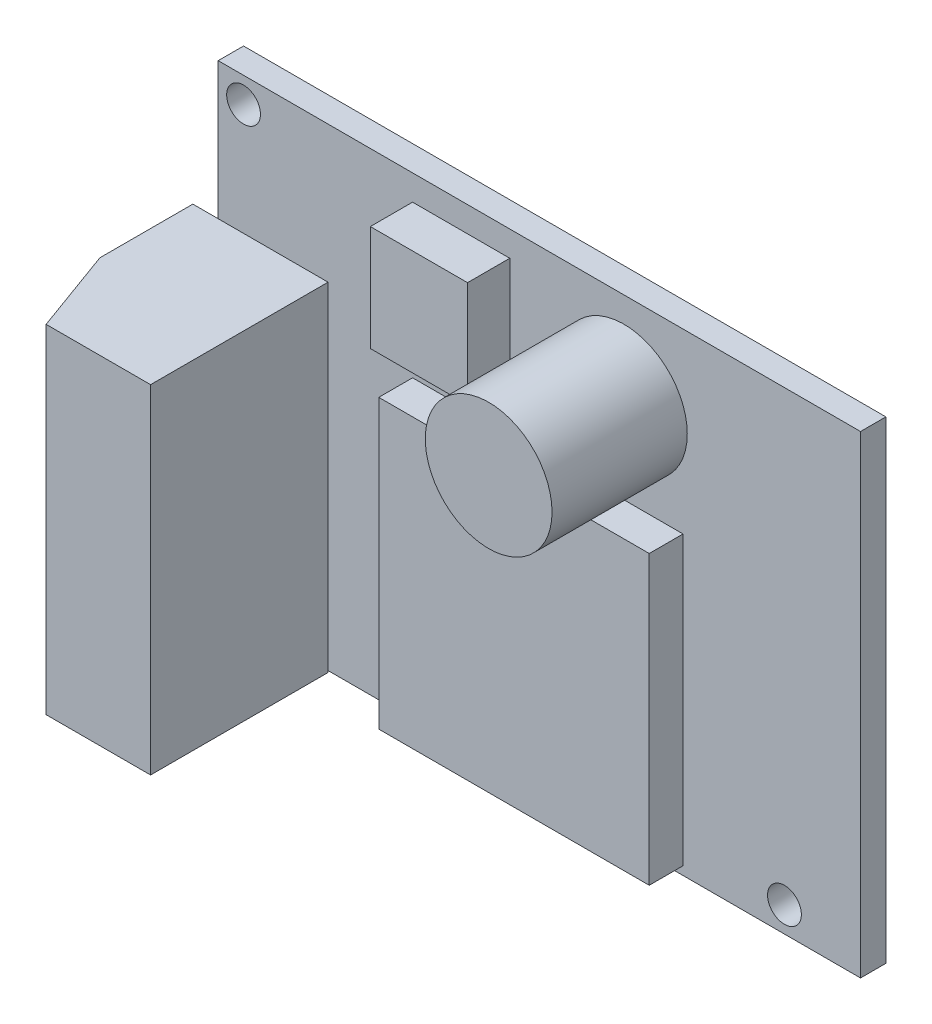
SolidWorks part; units mm, degrees
ref_plane "Front Plane" through (0, 0, 0) normal (0, 0, 1) x (1, 0, 0)
ref_plane "Top Plane" through (0, 0, 0) normal (0, 1, 0) x (1, 0, 0)
ref_plane "Right Plane" through (0, 0, 0) normal (1, 0, 0) x (0, 0, -1)
sketch "Sketch1" plane through (0, 0, 0) normal (0, 0, 1) x (1, 0, 0)
  line L1 (-19, 14) -> (19, 14)
  line L2 (-19, 14) -> (-19, -14)
  line L3 (-19, -14) -> (19, -14)
  line L4 (19, 14) -> (19, -14)
extrude "Boss-Extrude1" add sketch "Sketch1" along normal blind 1.5
sketch "Sketch2" plane through (0, 0, 1.5) normal (0, 0, 1) x (1, 0, 0)
  circle A0 centre (5, 8.75) radius 3.75
  point P8 (5, 8.75)
extrude "Boss-Extrude2" add sketch "Sketch2" along normal blind 8
sketch "Sketch3" plane through (0, 0, 1.5) normal (0, 0, 1) x (1, 0, 0)
  line L4 (-7.5, 12.5) -> (-1.75, 12.5)
  line L5 (-7.5, 12.5) -> (-7.5, 6.25)
  line L6 (-1.75, 12.5) -> (-1.75, 6.25)
  line L7 (-1.75, 6.25) -> (-7.5, 6.25)
  point P5 (-1.75, 6.25)
  point P8 (-7.5, 12.5)
  point P10 (-1.75, 12.5)
  point P12 (-7.5, 6.25)
extrude "Boss-Extrude3" add sketch "Sketch3" along normal blind 2.5
sketch "Sketch4" plane through (0, 0, 1.5) normal (0, 0, 1) x (1, 0, 0)
  line L4 (-7.5, -13.5) -> (-7.5, 3.5)
  line L5 (-7.5, 3.5) -> (8.5, 3.5)
  line L6 (8.5, 3.5) -> (8.5, -13.5)
  line L7 (8.5, -13.5) -> (-7.5, -13.5)
extrude "Boss-Extrude4" add sketch "Sketch4" along normal blind 2
sketch "Sketch5" plane through (0, 0, 1.5) normal (0, 0, 1) x (1, 0, 0)
  circle A0 centre (14.5, -12.5) radius 1
  dimension "D1" = 2
extrude "Cut-Extrude1" cut sketch "Sketch5" against normal blind 2
sketch "Sketch7" plane through (0, 0, 1.5) normal (0, 0, 1) x (1, 0, 0)
  circle A0 centre (-17.5, 12.5) radius 1
extrude "Cut-Extrude3" cut sketch "Sketch7" against normal blind 2
sketch "Sketch8" plane through (0, 0, 1.5) normal (0, 0, 1) x (1, 0, 0)
  line L0 (-19, 14) -> (-19, -14) construction
  line L1 (-12.5, 5.9) -> (-20.5, 5.9)
  line L2 (-12.5, 5.9) -> (-12.5, -14.1)
  line L3 (-12.5, -14.1) -> (-20.5, -14.1)
  line L4 (-20.5, 5.9) -> (-20.5, -14.1)
  line L7 (-19, -14) -> (19, -14) construction
  dimension "D1" = 20
  dimension "D2" = 8
  dimension "D3" = 1.5
  dimension "D4" = 0.1
extrude "Boss-Extrude5" add sketch "Sketch8" along normal blind 10.5
chamfer "Chamfer1" distance 5 angle 20 1 edges at (-20.5, -4.1, 12)
